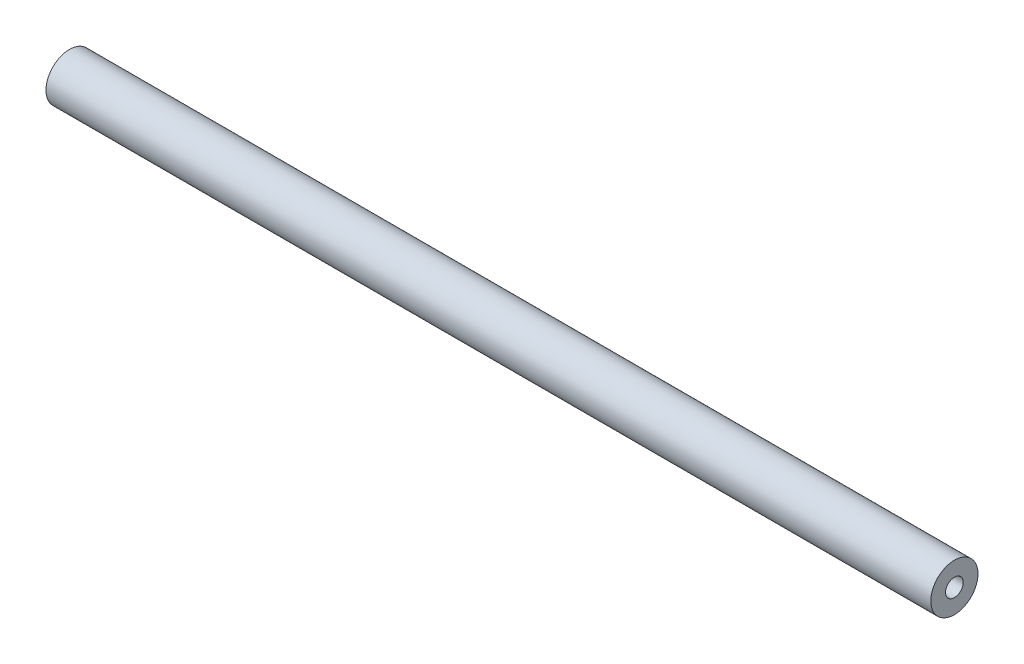
SolidWorks part; units mm, degrees
ref_plane "Front" through (0, 0, 0) normal (0, 0, 1) x (1, 0, 0)
ref_plane "Top" through (0, 0, 0) normal (0, 1, 0) x (1, 0, 0)
ref_plane "Right" through (0, 0, 0) normal (1, 0, 0) x (0, 0, -1)
sketch "Sketch1" plane through (0, 0, 0) normal (0, 0, 1) x (1, 0, 0)
  line L0 (0, 4) -> (0, 1.5)
  line L1 (0, 1.5) -> (149.86, 1.5)
  line L2 (149.86, 1.5) -> (149.86, 4)
  line L3 (149.86, 4) -> (0, 4)
  line L4 (0, 0) -> (150, 0) construction
  dimension "D1" = 150
revolve "Revolve1" add sketch "Sketch1" angle 360 about L4
